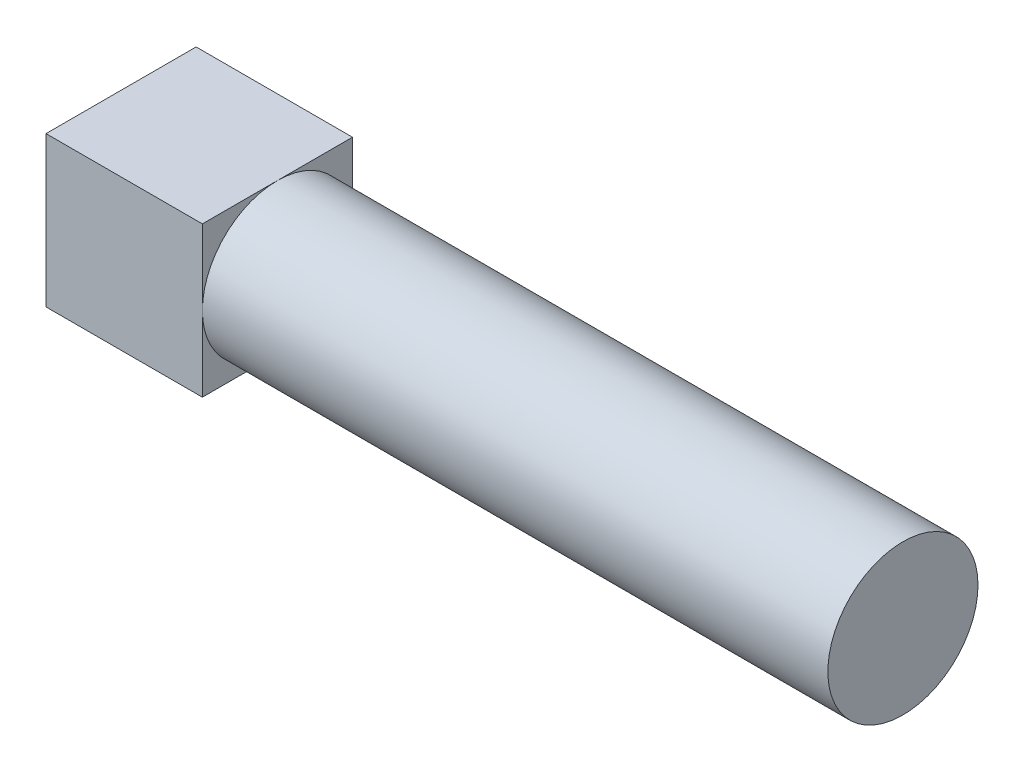
SolidWorks part; units mm, degrees
ref_plane "Front Plane" through (0, 0, 0) normal (0, 0, 1) x (1, 0, 0)
ref_plane "Top Plane" through (0, 0, 0) normal (0, 1, 0) x (1, 0, 0)
ref_plane "Right Plane" through (0, 0, 0) normal (1, 0, 0) x (0, 0, -1)
sketch "Sketch1" plane through (0, 0, 0) normal (1, 0, 0) x (0, 0, -1)
  line L1 (-4.8, 4.8) -> (4.8, 4.8)
  line L2 (-4.8, 4.8) -> (-4.8, -4.8)
  line L3 (-4.8, -4.8) -> (4.8, -4.8)
  line L4 (4.8, 4.8) -> (4.8, -4.8)
  line L5 (-4.8, 4.8) -> (4.8, -4.8) construction
  line L6 (-4.8, -4.8) -> (4.8, 4.8) construction
  point P0 (0, 0)
  dimension "D1" = 9.6
  dimension "D2" = 9.6
extrude "Boss-Extrude1" add sketch "Sketch1" along normal blind 10
sketch "Sketch2" plane through (10, 0, 0) normal (1, 0, 0) x (0, 0, -1)
  circle A0 centre (0, 0) radius 4.8
extrude "Boss-Extrude2" add sketch "Sketch2" along normal blind 40
